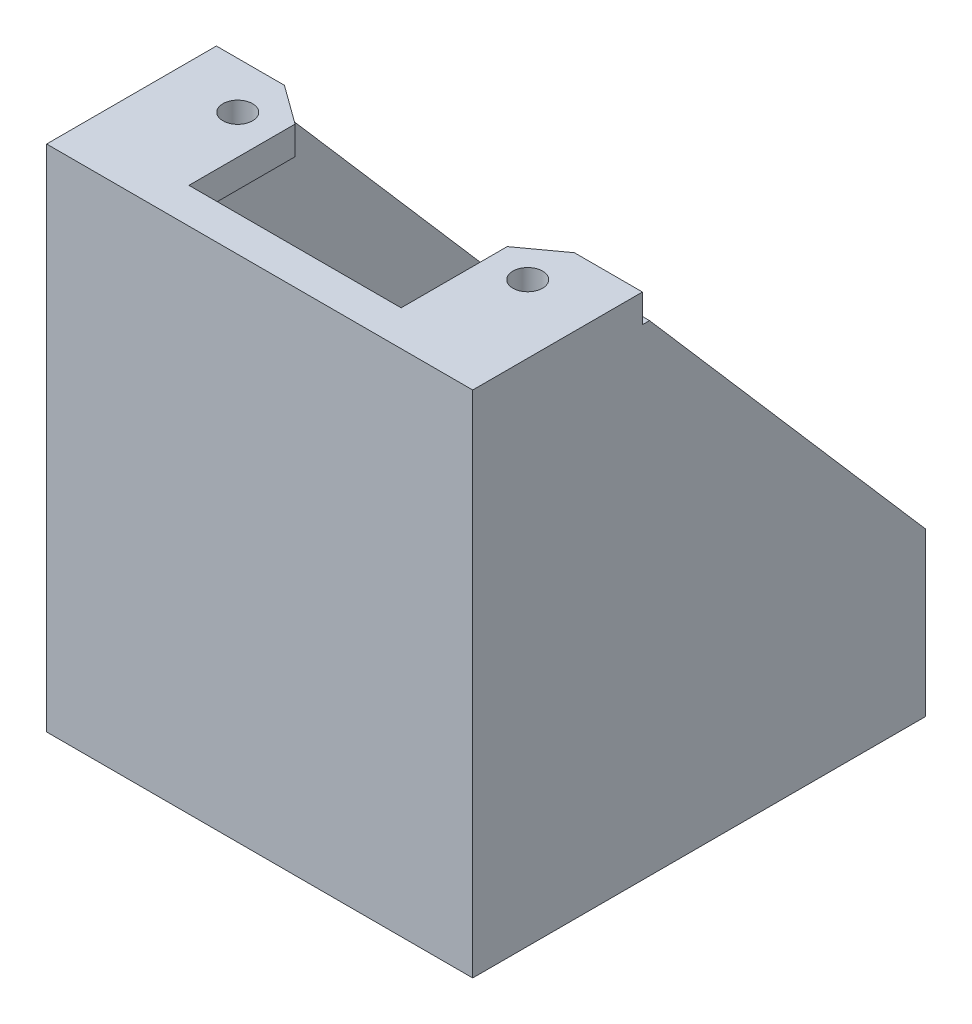
SolidWorks part; units mm, degrees
ref_plane "Front Plane" through (0, 0, 0) normal (0, 0, 1) x (1, 0, 0)
ref_plane "Top Plane" through (0, 0, 0) normal (0, 1, 0) x (1, 0, 0)
ref_plane "Right Plane" through (0, 0, 0) normal (1, 0, 0) x (0, 0, -1)
sketch "Sketch2" plane through (0, 0, 0) normal (0, 1, 0) x (1, 0, 0)
  line L0 (15.061, 0) -> (15.061, 32)
  line L1 (-12.561, 2.5) -> (12.561, 2.5)
  line L2 (-12.561, 2.5) -> (-12.561, 32)
  line L4 (12.561, 2.5) -> (12.561, 32)
  line L5 (15.061, 32) -> (12.561, 32)
  line L7 (-15.061, 32) -> (-15.061, 0)
  line L8 (-15.061, 0) -> (15.061, 0)
  line L10 (-15.061, 32) -> (-12.561, 32)
  point P4 (0, 2.5)
  point P12 (0, 0)
  dimension "D1" = 2.5
  dimension "D2" = 2.5
  dimension "D3" = 29.5
  dimension "D4" = 25.122
extrude "Boss-Extrude1" add sketch "Sketch2" along normal blind 32.5
sketch "Sketch3" plane through (15.061, 0, 0) normal (1, 0, 0) x (0, 0, -1)
  line L0 (32, 10) -> (12.5, 32.5)
  line L3 (12.5, 32.5) -> (32, 32.5)
  line L4 (32, 32.5) -> (32, 10)
  line L5 (0, 16.5671) -> (0, -16.5671) construction
  line L6 (32, 32.5) -> (32, 0) construction
  line L7 (0, 0) -> (32, 0) construction
  line L8 (0, 32.5) -> (32, 32.5) construction
  dimension "D1" = 10
  dimension "D2" = 12.5
extrude "Cut-Extrude1" cut sketch "Sketch3" against normal through all
sketch "Sketch4" plane through (0, 0, 0) normal (0, -1, 0) x (1, 0, 0)
  line L0 (-15.061, 0) -> (-15.061, -32)
  line L2 (-15.061, -32) -> (-10.061, -32)
  line L4 (-7.5, -6) -> (7.5, -6)
  line L6 (10.061, -32) -> (15.061, -32)
  line L8 (15.061, -32) -> (15.061, 0)
  line L9 (15.061, 0) -> (-15.061, 0)
  line L10 (15.061, 0) -> (15.061, -32) construction
  line L13 (-12.561, -2.5) -> (-12.561, -32) construction
  line L18 (-12.561, -10) -> (-7.5, -6)
  line L20 (-12.561, -10) -> (-12.561, -25)
  line L23 (12.561, -32) -> (12.561, -2.5) construction
  line L24 (12.561, -10) -> (12.561, -25)
  line L26 (12.561, -10) -> (7.5, -6)
  line L27 (-10.061, -32) -> (-8.061, -29.4695)
  line L28 (-8.061, -29.4695) -> (-12.561, -25)
  line L29 (10.061, -32) -> (8.061, -29.4695)
  line L31 (8.061, -29.4695) -> (12.561, -25)
  circle A2 centre (-10.2499, -4.95) radius 1.05
  circle A3 centre (-10.2499, -29.4) radius 1.05
  circle A4 centre (10.2499, -29.4) radius 1.05
  circle A5 centre (10.2499, -4.95) radius 1.05
  point P4 (0, 0)
  point P8 (-6.152, -27.0542)
  point P9 (0, 0)
  point P17 (5.06, -29.9759)
  point P19 (4.6005, -29.4)
  point P20 (6.3962, -29.4)
  point P31 (0, -6)
  dimension "D4" = 2
  dimension "D5" = 2.1
  dimension "D10" = 15
  dimension "D11" = 10
  dimension "D2" = 6
  dimension "D3" = 32
  dimension "D6" = 4.8111
  dimension "D7" = 4.95
  dimension "D8" = 4.8111
  dimension "D9" = 29.4
  dimension "D12" = 25
  dimension "D13" = 2
  dimension "D14" = 5
  dimension "D16" = 20.122
extrude "Boss-Extrude2" add sketch "Sketch4" along normal blind 1.5
sketch "Sketch5" plane through (0, 32.5, 0) normal (0, 1, 0) x (1, 0, 0)
  line L10 (-15.061, 12) -> (-10.2499, 12)
  line L11 (-10.2499, 12) -> (-7.5, 10)
  line L12 (-7.5, 10) -> (-7.5, 0)
  line L13 (-15.061, 0) -> (15.061, 0) construction
  line L14 (-7.5, 0) -> (-15.061, 0)
  line L15 (-15.061, 0) -> (-15.061, 12)
  line L16 (15.061, 12) -> (10.2499, 12)
  line L17 (10.2499, 12) -> (7.5, 10)
  line L18 (7.5, 10) -> (7.5, 0)
  line L19 (7.5, 0) -> (15.061, 0)
  line L20 (15.061, 0) -> (15.061, 12)
  circle A0 centre (-10.2499, 4.95) radius 1.05 construction
  circle A1 centre (-10.2499, 8.7) radius 1.05
  circle A2 centre (10.2499, 8.7) radius 1.05
  dimension "D4" = 0
  dimension "D1" = 8.7
  dimension "D2" = 15
  dimension "D3" = 20.4998
  dimension "D5" = 10
  dimension "D6" = 12
extrude "Boss-Extrude3" add sketch "Sketch5" along normal blind 2
fillet "Fillet1" radius 1 2 edges at (8.061, -0.75, -29.4695) (-8.061, -0.75, -29.4695)
sketch "Sketch6" plane through (0, 34.5, 0) normal (0, 1, 0) x (1, 0, 0)
  line L1 (-7.5, 0) -> (7.5, 0)
  line L2 (-7.5, 0) -> (-7.5, 2.5)
  line L3 (-7.5, 2.5) -> (7.5, 2.5)
  line L4 (7.5, 0) -> (7.5, 2.5)
extrude "Boss-Extrude4" add sketch "Sketch6" against normal up to surface (2 mm away) up to face at (-13.811, 32.5, -12.25)
